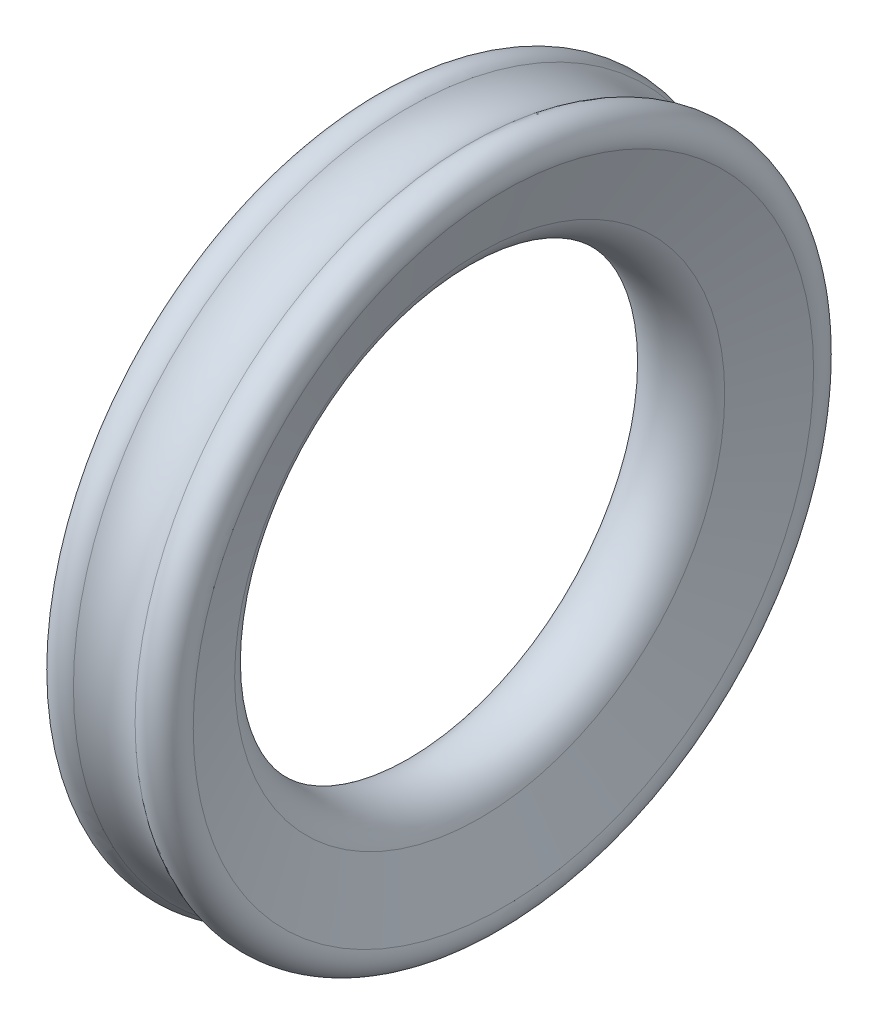
SolidWorks part; units mm, degrees
ref_plane "Front Plane" through (0, 0, 0) normal (0, 0, 1) x (1, 0, 0)
ref_plane "Top Plane" through (0, 0, 0) normal (0, 1, 0) x (1, 0, 0)
ref_plane "Right Plane" through (0, 0, 0) normal (1, 0, 0) x (0, 0, -1)
sketch "Sketch1" plane through (0, 0, 0) normal (0, 0, 1) x (1, 0, 0)
  line L0 (0, 0) -> (0, 36) construction
  line L1 (0, 0) -> (13.7183, 0) construction
  line L2 (5.6382, 33.9479) -> (8.9234, 42.9739)
  line L3 (-5.6382, 33.9479) -> (-8.9234, 42.9739)
  arc A0 (-5.6382, 33.9479) -> (5.6382, 33.9479) centre (0, 36) ccw
  arc A1 (8.9234, 42.9739) -> (4.273, 46.3762) centre (6.1043, 44) ccw
  arc A2 (-8.9234, 42.9739) -> (-4.273, 46.3762) centre (-6.1043, 44) cw
  arc A3 (-4.273, 46.3762) -> (4.273, 46.3762) centre (0, 51.9207) ccw
  dimension "D1" = 6
  dimension "D3" = 3
  dimension "D4" = 7
  dimension "D5" = 17
  dimension "D2" = 30
  dimension "D6" = 40
revolve "Revolve1" add sketch "Sketch1" angle 360 about L1
